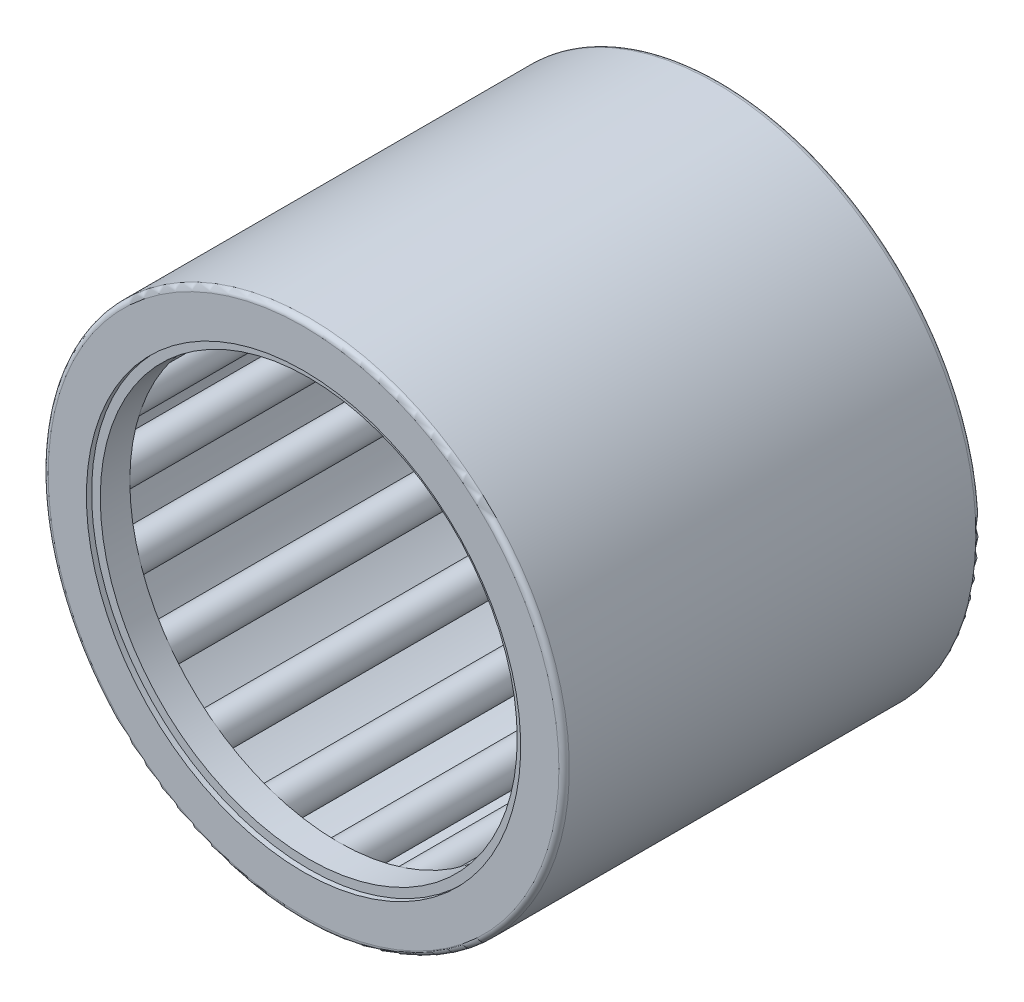
SolidWorks part; units mm, degrees
ref_plane "Front Plane" through (0, 0, 0) normal (0, 0, 1) x (1, 0, 0)
ref_plane "Top Plane" through (0, 0, 0) normal (0, 1, 0) x (1, 0, 0)
ref_plane "Right Plane" through (0, 0, 0) normal (1, 0, 0) x (0, 0, -1)
sketch "Sketch1" plane through (0, 0, 0) normal (1, 0, 0) x (0, 0, -1)
  line L0 (-12.7, 0) -> (12.7, 0) construction
  line L1 (0, 0) -> (0, 15.875) construction
  line L2 (-12.7, 0) -> (-12.7, 15.875) construction
  line L3 (-12.7, 15.875) -> (12.7, 15.875)
  line L4 (12.7, 15.875) -> (12.7, 0) construction
  line L5 (12.7, 0) -> (11.6417, 0) construction
  line L6 (11.6417, 0) -> (11.6417, 14.8167) construction
  line L7 (11.6417, 14.8167) -> (-11.6417, 14.8167)
  line L8 (-11.6417, 14.8167) -> (-11.6417, 0) construction
  line L9 (-11.6417, 0) -> (-12.7, 0) construction
  line L10 (-12.7, 15.875) -> (-12.7, 13.2292)
  line L11 (-12.7, 13.2292) -> (-11.6417, 13.2292)
  line L12 (-11.6417, 13.2292) -> (-11.6417, 14.8167)
  line L13 (11.6417, 15.875) -> (11.6417, 14.8167) construction
  line L14 (11.6417, 14.8167) -> (11.6417, 13.2292)
  line L15 (11.6417, 13.2292) -> (12.7, 13.2292)
  line L16 (12.7, 13.2292) -> (12.7, 15.875)
  line L17 (11.6417, 14.8167) -> (11.6417, 13.7583) construction
  line L18 (11.6417, 13.7583) -> (11.6417, 12.7) construction
  line L19 (11.6417, -14.8167) -> (11.6417, -13.7583) construction
  line L20 (11.6417, -15.875) -> (11.6417, -14.8167) construction
  line L21 (12.7, -13.2292) -> (12.7, -15.875) construction
  line L22 (11.6417, -13.2292) -> (12.7, -13.2292) construction
  line L23 (11.6417, -14.8167) -> (11.6417, -13.2292) construction
  line L24 (-11.6417, -13.2292) -> (-11.6417, -14.8167) construction
  line L25 (-12.7, -13.2292) -> (-11.6417, -13.2292) construction
  line L26 (-12.7, -15.875) -> (-12.7, -13.2292) construction
  line L27 (11.6417, -14.8167) -> (-11.6417, -14.8167) construction
  line L28 (-12.7, -15.875) -> (12.7, -15.875) construction
  point P5 (0, 12.7)
  dimension "Width" = 25.4
  dimension "OD" = 31.75
  dimension "Shaft Dia" = 25.4
revolve "Revolve1" add sketch "Sketch1" angle 360 about L0
sketch "Sketch2" plane through (0, 0, 0) normal (1, 0, 0) x (0, 0, -1)
  line L0 (11.6417, 14.8167) -> (-11.6417, 14.8167) construction
  line L1 (-10.5833, 13.7583) -> (10.5833, 13.7583) construction
  line L2 (-10.5833, 13.7583) -> (-10.5833, 14.8167) construction
  line L3 (-10.5833, 14.8167) -> (10.5833, 14.8167)
  line L4 (10.5833, 13.7583) -> (10.5833, 14.8167) construction
  line L5 (11.6417, 13.2292) -> (12.7, 13.2292) construction
  line L6 (-11.6417, 13.7583) -> (-10.5833, 13.7583) construction
  line L7 (10.5833, 13.7583) -> (11.6417, 13.7583) construction
  line L8 (-12.7, 13.2292) -> (-11.6417, 13.2292) construction
  line L9 (-10.5833, 14.0229) -> (-10.5833, 13.4937) construction
  line L10 (-11.6417, 13.7583) -> (-11.6417, 13.2292) construction
  line L11 (-10.5833, 14.8167) -> (-10.5833, 14.0229)
  line L12 (10.5833, 14.8167) -> (10.5833, 14.0229)
  line L13 (10.5833, 14.0229) -> (-10.5833, 14.0229)
  line L14 (0, 14.8167) -> (0, 12.7) construction
  line L15 (-11.6417, 13.2292) -> (-11.6417, 14.8167) construction
  line L16 (-10.5833, 13.4937) -> (-11.6417, 13.4937) construction
  line L17 (0, 0) -> (12.7, 0) construction
  line L18 (-10.5833, -13.4937) -> (-11.6417, -13.4937) construction
  line L19 (0, -14.8167) -> (0, -12.7) construction
  line L20 (-11.6417, -13.7583) -> (-11.6417, -13.2292) construction
  line L21 (-10.5833, -14.0229) -> (-10.5833, -13.4937) construction
  line L22 (10.5833, -13.7583) -> (11.6417, -13.7583) construction
  line L23 (-11.6417, -13.7583) -> (-10.5833, -13.7583) construction
  line L24 (10.5833, -13.7583) -> (10.5833, -14.8167) construction
  line L25 (-10.5833, -13.7583) -> (-10.5833, -14.8167) construction
  line L26 (-10.5833, -13.7583) -> (10.5833, -13.7583) construction
  line L27 (10.5833, -14.0229) -> (-10.5833, -14.0229) construction
  line L28 (10.5833, -14.8167) -> (10.5833, -14.0229) construction
  line L29 (-10.5833, -14.8167) -> (-10.5833, -14.0229) construction
  line L30 (-10.5833, -14.8167) -> (10.5833, -14.8167) construction
  line L31 (12.7, -15.875) -> (12.7, 15.875) construction
  point P16 (0, 13.7583)
revolve "Revolve2" add sketch "Sketch2" angle 360 about L1
sketch "Sketch3" plane through (0, 0, 0) normal (1, 0, 0) x (0, 0, -1)
  line L0 (11.6417, 14.8167) -> (11.6417, 13.2292) construction
  line L1 (-11.6417, 13.7583) -> (11.6417, 13.7583)
  line L2 (-11.6417, 13.7583) -> (-11.6417, 14.0229)
  line L3 (-11.6417, 14.0229) -> (11.6417, 14.0229)
  line L4 (11.6417, 13.7583) -> (11.6417, 14.0229)
  line L5 (0, 0) -> (12.7, 0) construction
  line L6 (12.7, -15.875) -> (12.7, 15.875) construction
  line L7 (11.6417, -13.7583) -> (11.6417, -14.0229) construction
  line L8 (-11.6417, -14.0229) -> (11.6417, -14.0229) construction
  line L9 (-11.6417, -13.7583) -> (-11.6417, -14.0229) construction
  line L10 (-11.6417, -13.7583) -> (11.6417, -13.7583) construction
revolve "Revolve3" add sketch "Sketch3" angle 360 about L1
ref_axis "Axis1" through (0, 0, -12.7) along (0, 0, 1)
pattern_circular "CirPattern1" count 20 every 18 about axis through (0, 0, -12.7) along (0, 0, 1) of bodies 166 167
fillet "Fillet1" radius 0.3175 2 edges at (0, -15.875, -12.7) (0, -15.875, 12.7)
sketch "Sketch4" plane through (0, 0, 0) normal (1, 0, 0) x (0, 0, -1)
  line L1 (12.3825, 12.7) -> (10.5833, 12.7)
  line L2 (12.3825, 12.7) -> (12.3825, 13.2292)
  line L3 (12.3825, 13.2292) -> (10.5833, 13.2292)
  line L4 (10.5833, 12.7) -> (10.5833, 13.2292)
  line L5 (-12.7, 13.2292) -> (-11.6417, 13.2292) construction
  line L6 (12.3825, -15.875) -> (12.3825, 15.875) construction
  line L7 (10.5833, 14.8167) -> (10.5833, 14.0229) construction
revolve "Revolve4" add sketch "Sketch4" angle 360 about L0
sketch "Sketch5" plane through (0, 0, 0) normal (1, 0, 0) x (0, 0, -1)
  line L0 (-12.3825, 15.875) -> (-12.3825, -15.875) construction
  line L1 (-10.5833, 12.7) -> (-12.3825, 12.7)
  line L2 (-10.5833, 12.7) -> (-10.5833, 13.2292)
  line L3 (-10.5833, 13.2292) -> (-12.3825, 13.2292)
  line L4 (-12.3825, 12.7) -> (-12.3825, 13.2292)
  line L6 (-10.5833, 14.8167) -> (-10.5833, 14.0229) construction
  line L7 (-12.7, 13.2292) -> (-11.6417, 13.2292) construction
revolve "Revolve5" add sketch "Sketch5" angle 360 about L0
equation "\"Angle@CirPattern1\" = 360/\"Rollers@CirPattern1\""
equation "\"Rollers@CirPattern1\" = \"OD@Sketch1\"*16"
equation "\"D1@Fillet1\" = \"OD@Sketch1\"*.01"
